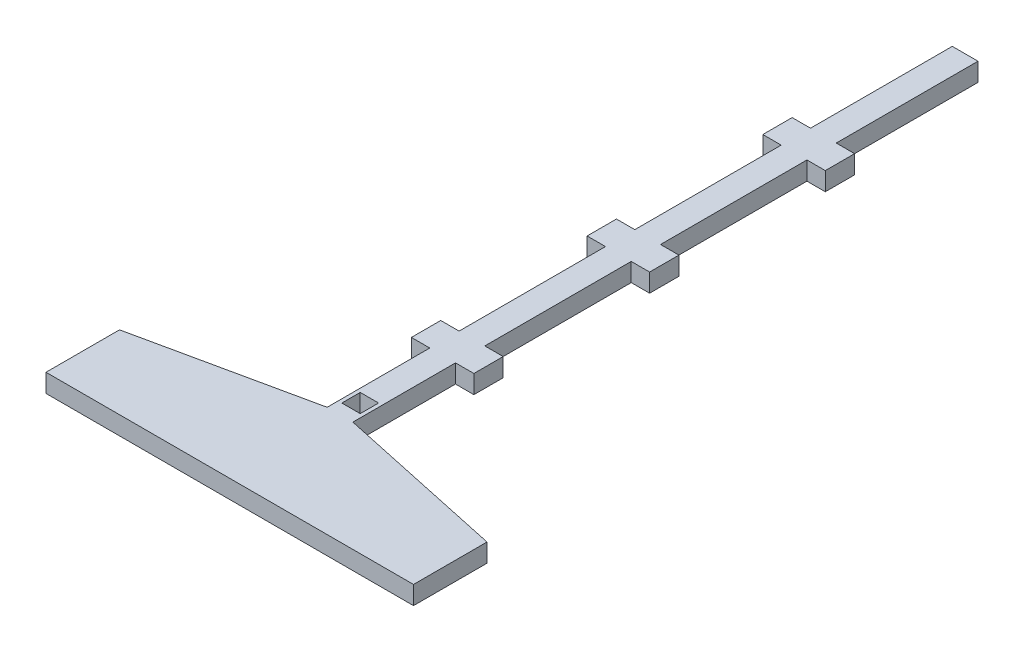
SolidWorks part; units mm, degrees
ref_plane "Front Plane" through (0, 0, 0) normal (0, 0, 1) x (1, 0, 0)
ref_plane "Top Plane" through (0, 0, 0) normal (0, 1, 0) x (1, 0, 0)
ref_plane "Right Plane" through (0, 0, 0) normal (1, 0, 0) x (0, 0, -1)
sketch "Sketch1" plane through (0, 0, 0) normal (0, 1, 0) x (1, 0, 0)
  line L0 (0, 0) -> (127, 0)
  line L1 (0, 0) -> (0, 25.4)
  line L2 (127, 0) -> (127, 25.4)
  line L3 (63.5, 0) -> (63.5, 301.7359) construction
  line L4 (0, 25.4) -> (0, 38.1) construction
  line L5 (0, 38.1) -> (127, 38.1) construction
  line L6 (127, 38.1) -> (127, 25.4) construction
  line L7 (67.945, 38.1) -> (59.055, 38.1) construction
  line L8 (0, 25.4) -> (59.055, 38.1)
  line L9 (67.945, 38.1) -> (127, 25.4)
  line L10 (59.055, 38.1) -> (59.055, 73.5668)
  line L11 (59.055, 73.5668) -> (52.705, 73.5668)
  line L12 (52.705, 73.5668) -> (52.705, 83.6987)
  line L13 (59.055, 38.1) -> (59.055, 160.2656) construction
  line L14 (52.705, 83.6987) -> (59.055, 83.6987)
  line L15 (59.055, 83.6987) -> (59.055, 134.2887)
  line L16 (59.055, 134.2887) -> (52.705, 134.2887)
  line L17 (52.705, 134.2887) -> (52.705, 144.4205)
  line L18 (52.705, 144.4205) -> (59.055, 144.4205)
  line L19 (59.055, 144.4205) -> (59.055, 195.0105)
  line L20 (59.055, 195.0105) -> (59.055, 301.6983) construction
  line L21 (59.055, 195.0105) -> (52.705, 195.0105)
  line L22 (52.705, 195.0105) -> (52.705, 205.1424)
  line L23 (52.705, 205.1424) -> (59.055, 205.1424)
  line L24 (59.055, 205.1424) -> (59.055, 254.1268)
  line L25 (59.055, 254.1268) -> (67.945, 254.1268)
  line L26 (67.945, 38.1) -> (67.945, 73.5668)
  line L27 (67.945, 73.5668) -> (74.295, 73.5668)
  line L28 (74.295, 73.5668) -> (74.295, 83.6987)
  line L29 (74.295, 83.6987) -> (67.945, 83.6987)
  line L30 (67.945, 83.6987) -> (67.945, 134.2887)
  line L31 (67.945, 134.2887) -> (74.295, 134.2887)
  line L32 (74.295, 134.2887) -> (74.295, 144.4205)
  line L33 (74.295, 144.4205) -> (67.945, 144.4205)
  line L34 (67.945, 144.4205) -> (67.945, 195.0105)
  line L35 (67.945, 195.0105) -> (74.295, 195.0105)
  line L36 (74.295, 195.0105) -> (74.295, 205.1424)
  line L37 (74.295, 205.1424) -> (67.945, 205.1424)
  line L38 (67.945, 205.1424) -> (67.945, 254.1268)
  line L39 (63.5, 38.1) -> (63.5, 48.26) construction
  line L40 (66.675, 48.26) -> (60.325, 48.26)
  line L41 (60.325, 48.26) -> (60.325, 41.91)
  line L42 (60.325, 41.91) -> (66.675, 41.91)
  line L43 (66.675, 41.91) -> (66.675, 48.26)
  point P12 (63.5, 38.1)
  point P41 (63.5, 254.1268)
  point P46 (63.5, 48.26)
  dimension "D2" = 25.4
  dimension "D3" = 12.7
  dimension "D4" = 127
  dimension "D5" = 8.89
  dimension "D6" = 35.4668
  dimension "D7" = 6.35
  dimension "D8" = 10.1319
  dimension "D9" = 50.59
  dimension "D10" = 6.35
  dimension "D11" = 10.1319
  dimension "D12" = 50.59
  dimension "D13" = 6.35
  dimension "D14" = 10.1319
  dimension "D15" = 48.9844
  dimension "D16" = 10.16
  dimension "D17" = 6.35
  dimension "D18" = 6.35
extrude "Boss-Extrude2" add sketch "Sketch1" along normal blind 6.35
